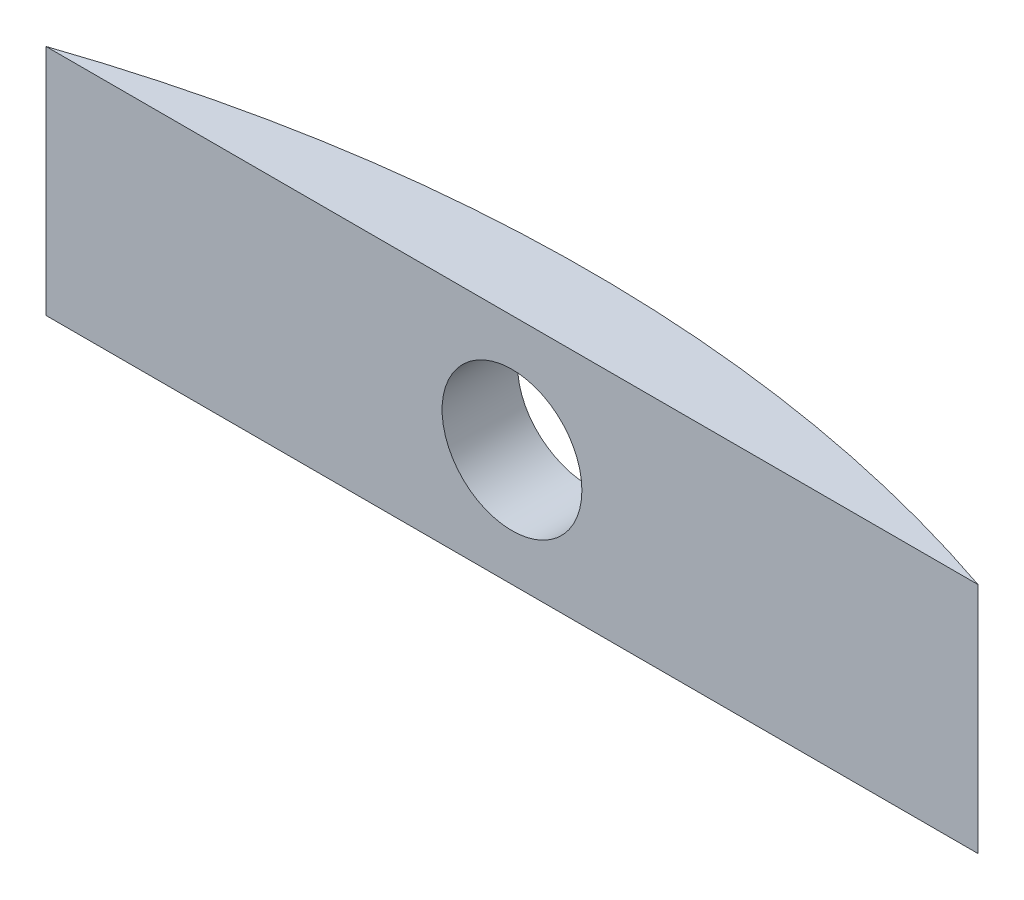
SolidWorks part; units mm, degrees
ref_plane "Front Plane" through (0, 0, 0) normal (0, 0, 1) x (1, 0, 0)
ref_plane "Top Plane" through (0, 0, 0) normal (0, 1, 0) x (1, 0, 0)
ref_plane "Right Plane" through (0, 0, 0) normal (1, 0, 0) x (0, 0, -1)
sketch "Sketch1" plane through (0, 0, 0) normal (0, 1, 0) x (1, 0, 0)
  line L0 (0, 0) -> (40, 0)
  arc A1 (0, 0) -> (40, 0) centre (20, -58.6856) cw
extrude "Boss-Extrude1" add sketch "Sketch1" along normal blind 10 contours A1 L0
sketch "Sketch2" plane through (0, 0, 0) normal (0, 0, 1) x (1, 0, 0)
  line L0 (20, 0) -> (20, 10) construction
  line L1 (0, 0) -> (40, 0) construction
  line L2 (0, 10) -> (40, 10) construction
  circle A0 centre (20, 5) radius 3
extrude "Cut-Extrude1" cut sketch "Sketch2" against normal up to next contours A0
